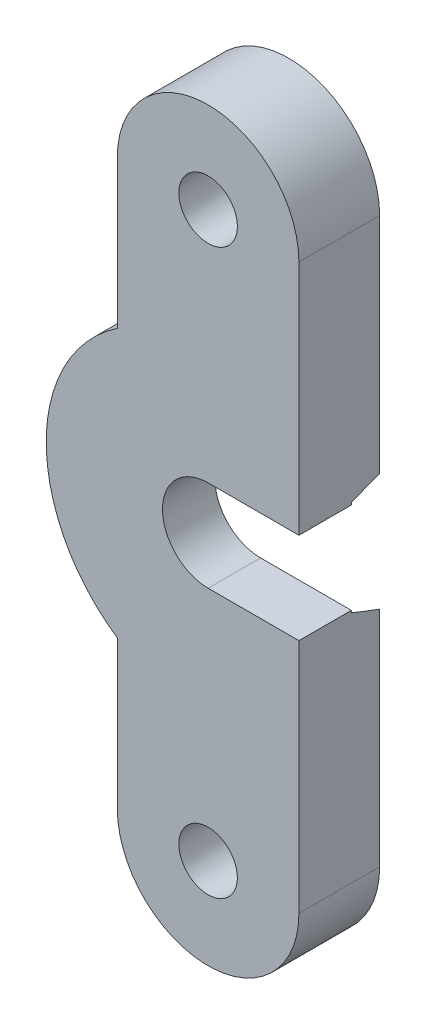
SolidWorks part; units mm, degrees
ref_plane "Front Plane" through (0, 0, 0) normal (0, 0, 1) x (1, 0, 0)
ref_plane "Top Plane" through (0, 0, 0) normal (0, 1, 0) x (1, 0, 0)
ref_plane "Right Plane" through (0, 0, 0) normal (1, 0, 0) x (0, 0, -1)
sketch "Sketch1" plane through (0, 0, 0) normal (0, 0, 1) x (1, 0, 0)
  line L0 (-19, 6.632) -> (-19, 13.975)
  line L2 (-19, -13.975) -> (-19, -6.652)
  line L4 (-10, -13.975) -> (-10, 13.975)
  arc A0 (-19, -13.975) -> (-10, -13.975) centre (-14.5, -13.975) ccw
  arc A1 (-10, 13.975) -> (-19, 13.975) centre (-14.5, 13.975) ccw
  circle A2 centre (-14.5, -13.975) radius 1.45
  circle A3 centre (-14.5, 13.975) radius 1.45
  arc A4 (-19, 6.632) -> (-19, -6.652) centre (-14.5, -0.01) ccw
  dimension "D1" = 2.9
extrude "Boss-Extrude1" add sketch "Sketch1" along normal blind 4
sketch "Sketch2" plane through (0, 0, 0) normal (0, 0, -1) x (-1, 0, 0)
  circle A0 centre (14.5, -0.01) radius 5.3561
extrude "Cut-Extrude1" cut sketch "Sketch2" against normal blind 1.4 draft 11
sketch "Sketch3" plane through (0, 0, 4) normal (0, 0, 1) x (1, 0, 0)
  line L0 (-10, -13.975) -> (-10, 13.975) construction
  line L1 (-14.5, -2.2702) -> (-10, -2.2702)
  line L3 (-14.5, 2.2502) -> (-10, 2.2502)
  line L4 (-10, -2.2702) -> (-10, 2.2502)
  arc A0 (-14.5, 2.2502) -> (-14.5, -2.2702) centre (-14.5, -0.01) ccw
extrude "Cut-Extrude2" cut sketch "Sketch3" against normal blind 5.5
